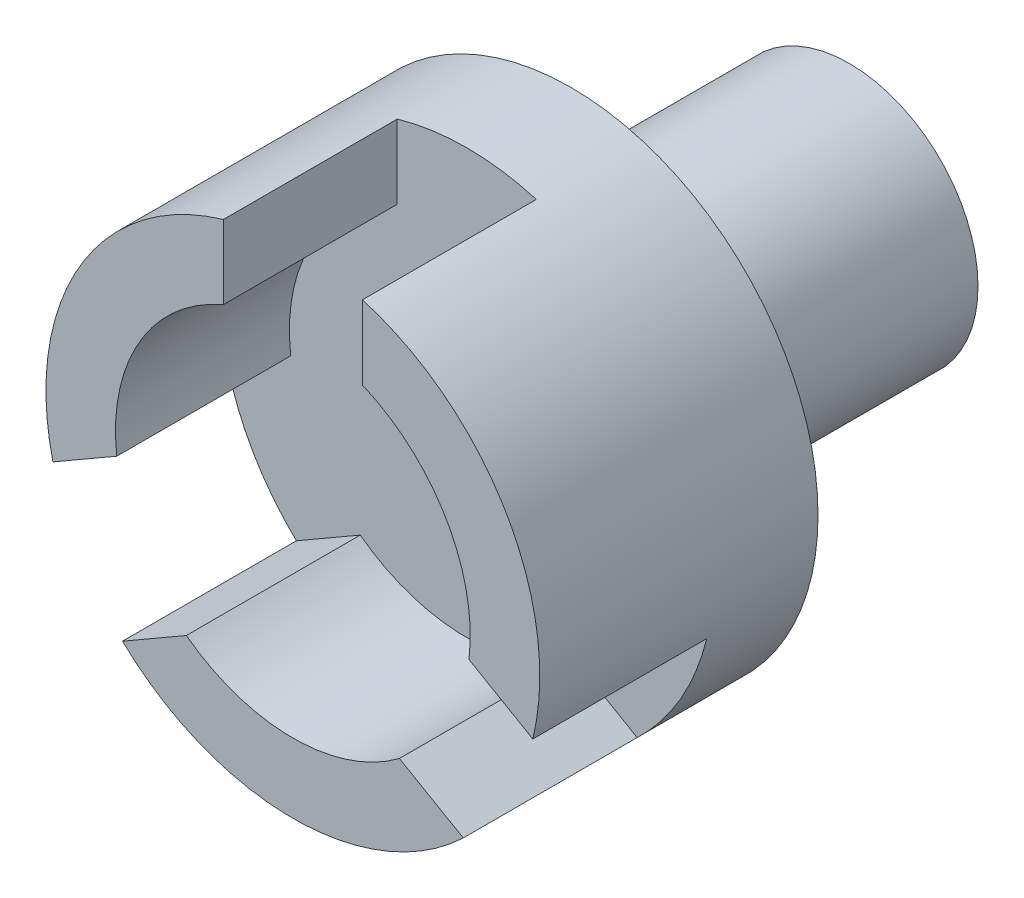
SolidWorks part; units mm, degrees
ref_plane "前视基准面" through (0, 0, 0) normal (0, 0, 1) x (1, 0, 0)
ref_plane "上视基准面" through (0, 0, 0) normal (0, 1, 0) x (1, 0, 0)
ref_plane "右视基准面" through (0, 0, 0) normal (1, 0, 0) x (0, 0, -1)
other "Configuration Table"
sketch "草图1" plane through (0, 0, 0) normal (0, 0, 1) x (1, 0, 0)
  circle A0 centre (-2.7632, 3.5646) radius 5.1 construction
  circle A1 centre (-2.7632, 3.5646) radius 7.1
  dimension "D1" = 10.2
  dimension "D2" = 2
extrude "凸台-拉伸1" add sketch "草图1" along normal blind 8
sketch "草图2" plane through (0, 0, 0) normal (0, 0, -1) x (-1, 0, 0)
  circle A0 centre (2.7632, 3.5646) radius 1.7
  dimension "D1" = 3.4
extrude "切除-拉伸1" cut sketch "草图2" against normal blind 6
sketch "草图3" plane through (0, 0, 8) normal (0, 0, 1) x (1, 0, 0)
  circle A0 centre (-2.7632, 3.5646) radius 5.1
extrude "切除-拉伸2" cut sketch "草图3" against normal blind 5
sketch "草图4" plane through (0, 0, 0) normal (0, 0, -1) x (-1, 0, 0)
  circle A0 centre (2.7632, 3.5646) radius 3.7
  circle A1 centre (2.7632, 3.5646) radius 1.7
  circle A2 centre (2.7632, 3.5646) radius 1.7 construction
  circle M2 centre (2.7632, 3.5646) radius 1.7
  dimension "D1" = 2
extrude "凸台-拉伸2" add sketch "草图4" along normal blind 8 contours A0 M2 | A1
sketch "草图5" plane through (0, 0, 8) normal (0, 0, 1) x (1, 0, 0)
  line L0 (-2.7632, 3.5646) -> (-2.7632, 10.6646) construction
  line L1 (-2.7632, 3.5646) -> (-8.912, 0.0146) construction
  line L2 (-2.7632, 3.5646) -> (3.3856, 0.0146) construction
  line L3 (-0.7632, 4.7193) -> (-0.7632, 10.377)
  line L5 (-4.7632, 4.7193) -> (-9.663, 1.8904)
  line L6 (-4.7632, 4.7193) -> (-4.7632, 10.377)
  line L7 (-0.7632, 4.7193) -> (4.1366, 1.8904)
  line L9 (-3.7632, 5.2966) -> (-9.912, 1.7466) construction
  line L11 (-1.7632, 5.2966) -> (4.3856, 1.7466) construction
  line L13 (-0.7632, 3.5646) -> (-0.7632, 10.6646) construction
  line L14 (-4.7632, 3.5646) -> (-4.7632, 10.6646) construction
  line L15 (-2.7632, 1.2552) -> (-7.663, -1.5737)
  line L16 (-2.7632, 1.2552) -> (2.1366, -1.5737)
  circle A0 centre (-2.7632, 3.5646) radius 7.1 construction
  arc A1 (-3.9436, 5.1924) -> (-1.9436, 1.7283) centre (-2.7632, 3.5646) ccw
  arc A3 (-9.663, 1.8904) -> (-7.663, -1.5737) centre (-2.7632, 3.5646) ccw
  arc A4 (2.1366, -1.5737) -> (4.1366, 1.8904) centre (-2.7632, 3.5646) ccw
  arc A5 (-0.7632, 10.377) -> (-4.7632, 10.377) centre (-2.7632, 3.5646) ccw
  arc A6 (-3.5828, 1.7283) -> (-1.5828, 5.1924) centre (-2.7632, 3.5646) ccw
  arc A7 (-0.7632, 3.7729) -> (-4.7632, 3.7729) centre (-2.7632, 3.5646) ccw
  point P24 (-9.3507, 0.916)
  point P27 (-8.3507, -0.8161)
  point P30 (3.8243, 0.916)
  point P33 (2.8243, -0.8161)
  point P36 (-1.7632, 10.5938)
  point P39 (-3.7632, 10.5938)
  dimension "D5" = 2
  dimension "D1" = 120
  dimension "D2" = 120
  dimension "D6" = 2
  dimension "D7" = 2
  dimension "D3" = 2
  dimension "D4" = 2
extrude "切除-拉伸4" cut sketch "草图5" against normal blind 5 contours L15 A3 L5 L6 A5 L3 L7 A4 L16
